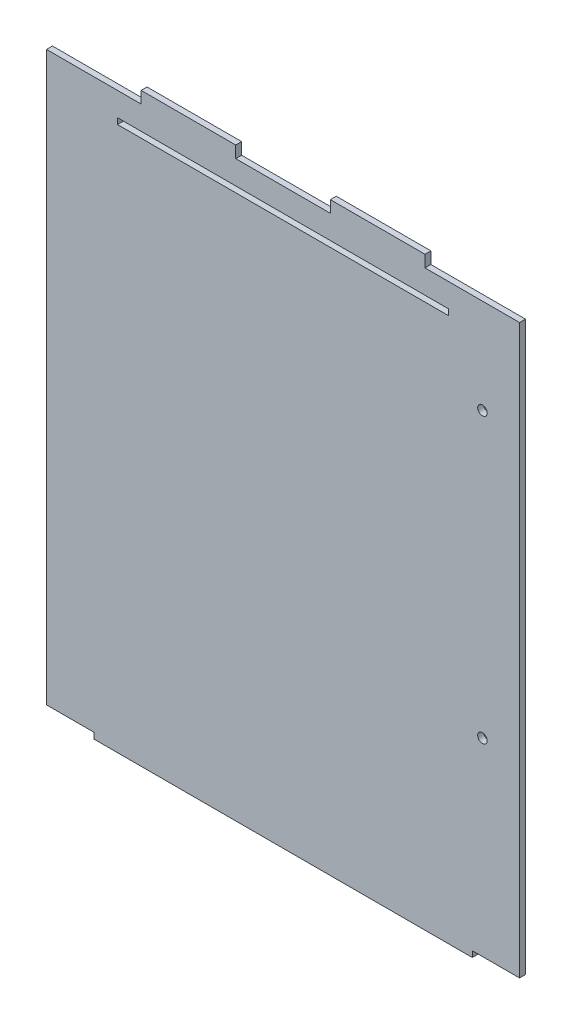
SolidWorks part; units mm, degrees
ref_plane "Front Plane" through (0, 0, 0) normal (0, 0, 1) x (1, 0, 0)
ref_plane "Top Plane" through (0, 0, 0) normal (0, 1, 0) x (1, 0, 0)
ref_plane "Right Plane" through (0, 0, 0) normal (1, 0, 0) x (0, 0, -1)
sketch "Sketch1" plane through (0, 0, 0) normal (0, 0, 1) x (1, 0, 0)
  line L0 (0, -3.175) -> (25.4, -3.175)
  line L1 (25.4, -6.35) -> (228.6, -6.35)
  line L2 (0, -3.175) -> (0, 301.625)
  line L3 (50.8, 307.975) -> (101.6, 307.975)
  line L4 (254, -3.175) -> (254, 301.625)
  line L5 (25.4, -3.175) -> (25.4, -6.35)
  line L6 (25.4, -6.35) -> (228.6, -6.35)
  line L7 (0, 301.625) -> (50.8, 301.625)
  line L8 (50.8, 301.625) -> (50.8, 307.975)
  line L9 (50.8, 307.975) -> (101.6, 307.975)
  line L10 (101.6, 307.975) -> (101.6, 301.625)
  line L11 (101.6, 301.625) -> (152.4, 301.625)
  line L12 (152.4, 301.625) -> (152.4, 307.975)
  line L13 (152.4, 307.975) -> (203.2, 307.975)
  line L14 (203.2, 307.975) -> (203.2, 301.625)
  line L15 (203.2, 301.625) -> (254, 301.625)
  line L16 (152.4, 307.975) -> (203.2, 307.975)
  line L17 (228.6, -6.35) -> (228.6, -3.175)
  line L18 (228.6, -3.175) -> (254, -3.175)
  line L20 (38.1, 288.925) -> (215.9, 288.925)
  line L21 (38.1, 288.925) -> (38.1, 285.75)
  line L22 (38.1, 285.75) -> (215.9, 285.75)
  line L23 (215.9, 288.925) -> (215.9, 285.75)
  dimension "D1" = 314.325
  dimension "D2" = 3.175
  dimension "D3" = 6.35
  dimension "D4" = 50.8
  dimension "D5" = 50.8
  dimension "D6" = 50.8
  dimension "D7" = 50.8
  dimension "D8" = 50.8
  dimension "D9" = 3.175
  dimension "D10" = 25.4
  dimension "D11" = 25.4
  dimension "D12" = 3.175
  dimension "D13" = 177.8
  dimension "D14" = 38.1
  dimension "D15" = 12.7
extrude "Boss-Extrude1" add sketch "Sketch1" along normal blind 3.175 contours L17 L18 L4 L15 L14 L13 L12 L11 L10 L3 L8 L7 L2 L0 L5 L1 L20 L23 L22 L21
sketch "Sketch2" plane through (0, 0, 0) normal (0, 0, -1) x (-1, 0, 0)
  line L0 (-228.6, -3.175) -> (-254, -3.175) construction
  circle A0 centre (-234.0633, 250.825) radius 2.54
  circle A1 centre (-234.0633, 98.425) radius 2.54
  dimension "D1" = 5.08
  dimension "D2" = 101.6
  dimension "D3" = 152.4
extrude "Cut-Extrude1" cut sketch "Sketch2" against normal through all
